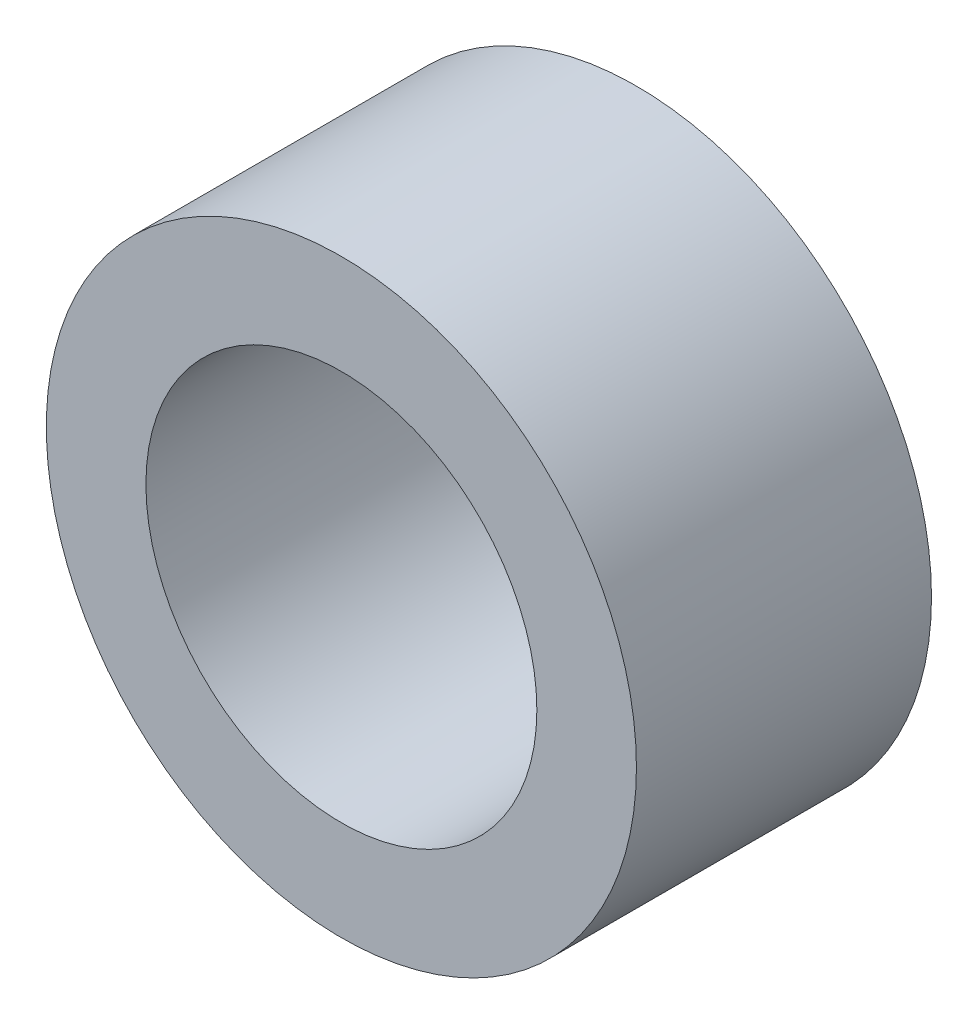
SolidWorks part; units mm, degrees
ref_plane "Front Plane" through (0, 0, 0) normal (0, 0, 1) x (1, 0, 0)
ref_plane "Top Plane" through (0, 0, 0) normal (0, 1, 0) x (1, 0, 0)
ref_plane "Right Plane" through (0, 0, 0) normal (1, 0, 0) x (0, 0, -1)
sketch "Sketch1" plane through (0, 0, 0) normal (0, 0, 1) x (1, 0, 0)
  line L0 (0, 2.65) -> (0, 4) construction
  line L1 (0, -2.65) -> (0, -4) construction
  circle A0 centre (0, 0) radius 4
  circle A1 centre (0, 0) radius 2.65
  dimension "OD" = 8
  dimension "ID" = 5.3
sketch "Sketch2" plane through (0, 0, 0) normal (1, 0, 0) x (0, 0, -1)
  line L0 (-2, 2.65) -> (2, 2.65) construction
  line L1 (-2, -2.65) -> (2, -2.65) construction
  line L2 (-2, -4) -> (2, -4) construction
  line L3 (-2, 4) -> (2, 4) construction
  dimension "Length" = 4
extrude "Extrude1" add sketch "Sketch1" along normal up to vertex (2 mm away) and the other way up to vertex (2 mm away) up to point (0, 2.65, 2) other way up to point (0, 2.65, -2)
sketch "Sketch3" plane through (0, 0, 2) normal (0, 0, 1) x (1, 0, 0)
  circle A0 centre (0, 0) radius 2.65 construction
  circle A3 centre (0, 0) radius 2.65
  point P3 (-2.65, 0)
